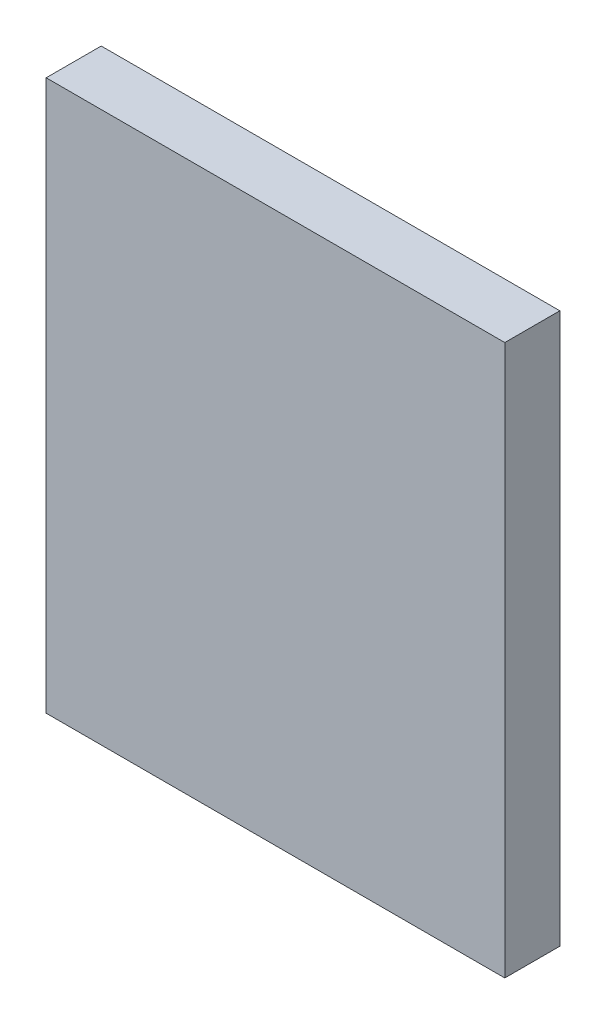
SolidWorks part; units mm, degrees
ref_plane "前视基准面" through (0, 0, 0) normal (0, 0, 1) x (1, 0, 0)
ref_plane "上视基准面" through (0, 0, 0) normal (0, 1, 0) x (1, 0, 0)
ref_plane "右视基准面" through (0, 0, 0) normal (1, 0, 0) x (0, 0, -1)
sketch "草图1" plane through (0, 0, 0) normal (0, 0, 1) x (1, 0, 0)
  line L1 (-20.8817, 8.9907) -> (29.1183, 8.9907)
  line L2 (-20.8817, 8.9907) -> (-20.8817, -51.0093)
  line L3 (-20.8817, -51.0093) -> (29.1183, -51.0093)
  line L4 (29.1183, 8.9907) -> (29.1183, -51.0093)
  dimension "D1" = 50
  dimension "D2" = 60
extrude "凸台-拉伸1" add sketch "草图1" along normal blind 6 contours L2 L1 L4 L3
